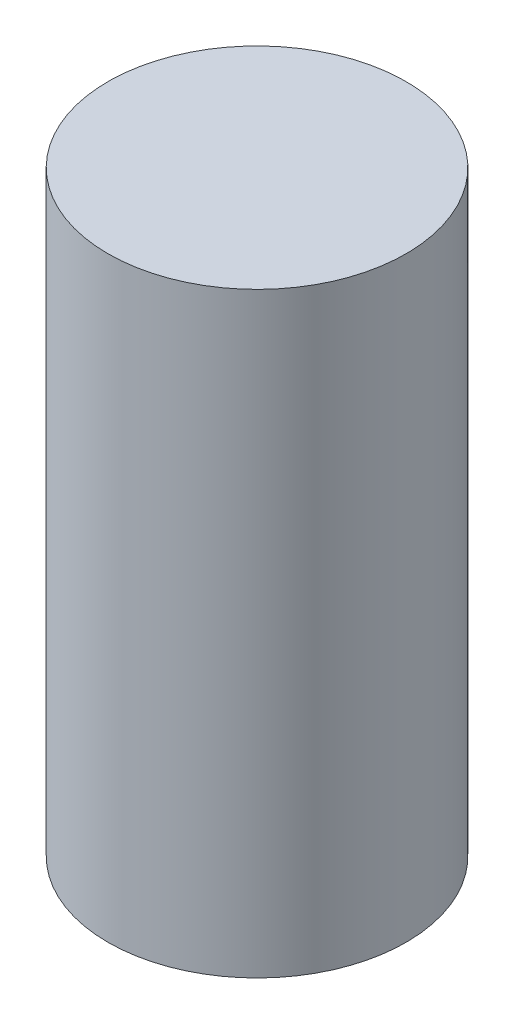
SolidWorks part; units mm, degrees
ref_plane "Front Plane" through (0, 0, 0) normal (0, 0, 1) x (1, 0, 0)
ref_plane "Top Plane" through (0, 0, 0) normal (0, 1, 0) x (1, 0, 0)
ref_plane "Right Plane" through (0, 0, 0) normal (1, 0, 0) x (0, 0, -1)
sketch "Sketch1" plane through (0, 0, 0) normal (0, 1, 0) x (1, 0, 0)
  circle A0 centre (0, 0) radius 10
  dimension "D1" = 20
extrude "Extrude1" add sketch "Sketch1" along normal blind 40
